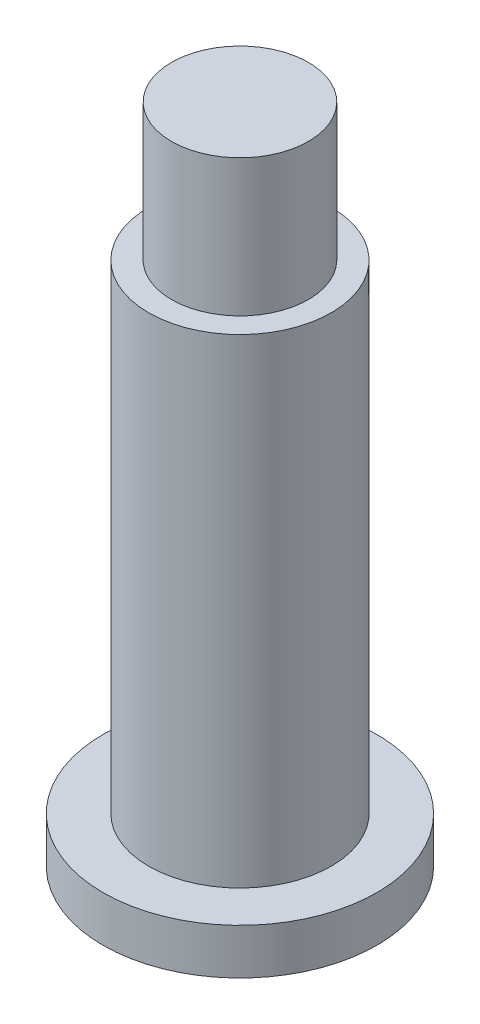
SolidWorks part; units mm, degrees
ref_plane "前视基准面" through (0, 0, 0) normal (0, 0, 1) x (1, 0, 0)
ref_plane "上视基准面" through (0, 0, 0) normal (0, 1, 0) x (1, 0, 0)
ref_plane "右视基准面" through (0, 0, 0) normal (1, 0, 0) x (0, 0, -1)
sketch "草图1" plane through (0, 0, 0) normal (0, 1, 0) x (1, 0, 0)
  circle A0 centre (0, 0) radius 6
  dimension "D1" = 12
extrude "凸台-拉伸1" add sketch "草图1" along normal blind 2
sketch "草图2" plane through (0, 2, 0) normal (0, 1, 0) x (1, 0, 0)
  circle A0 centre (0, 0) radius 4
  dimension "D1" = 8
extrude "凸台-拉伸2" add sketch "草图2" along normal blind 21
sketch "草图3" plane through (0, 23, 0) normal (0, 1, 0) x (1, 0, 0)
  circle A0 centre (0, 0) radius 3
  dimension "D1" = 6
extrude "凸台-拉伸3" add sketch "草图3" along normal blind 6
cosmetic thread "装饰螺纹线1" parameters "D1"=6, "D2"=5
